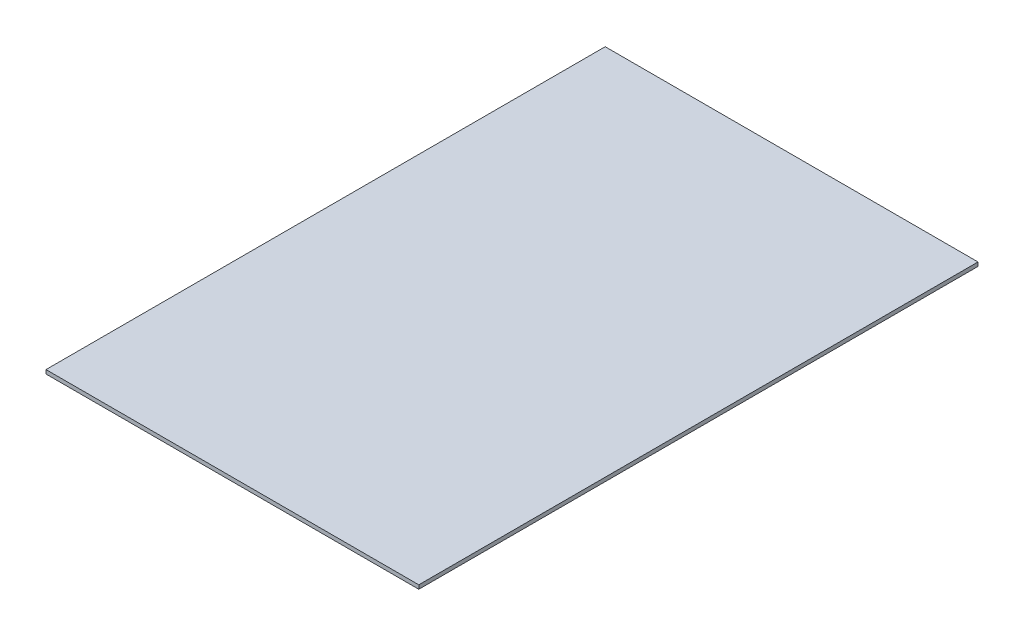
SolidWorks part; units mm, degrees
ref_plane "Front Plane" through (0, 0, 0) normal (0, 0, 1) x (1, 0, 0)
ref_plane "Top Plane" through (0, 0, 0) normal (0, 1, 0) x (1, 0, 0)
ref_plane "Right Plane" through (0, 0, 0) normal (1, 0, 0) x (0, 0, -1)
sketch "Sketch1" plane through (0, 0, 0) normal (0, 1, 0) x (1, 0, 0)
  line L1 (304.8, 457.2) -> (-304.8, 457.2)
  line L2 (304.8, 457.2) -> (304.8, -457.2)
  line L3 (304.8, -457.2) -> (-304.8, -457.2)
  line L4 (-304.8, 457.2) -> (-304.8, -457.2)
  line L5 (304.8, 457.2) -> (-304.8, -457.2) construction
  line L6 (304.8, -457.2) -> (-304.8, 457.2) construction
  point P0 (0, 0)
  dimension "D1" = 609.6
  dimension "D2" = 914.4
extrude "Boss-Extrude1" add sketch "Sketch1" along normal blind 6.35
